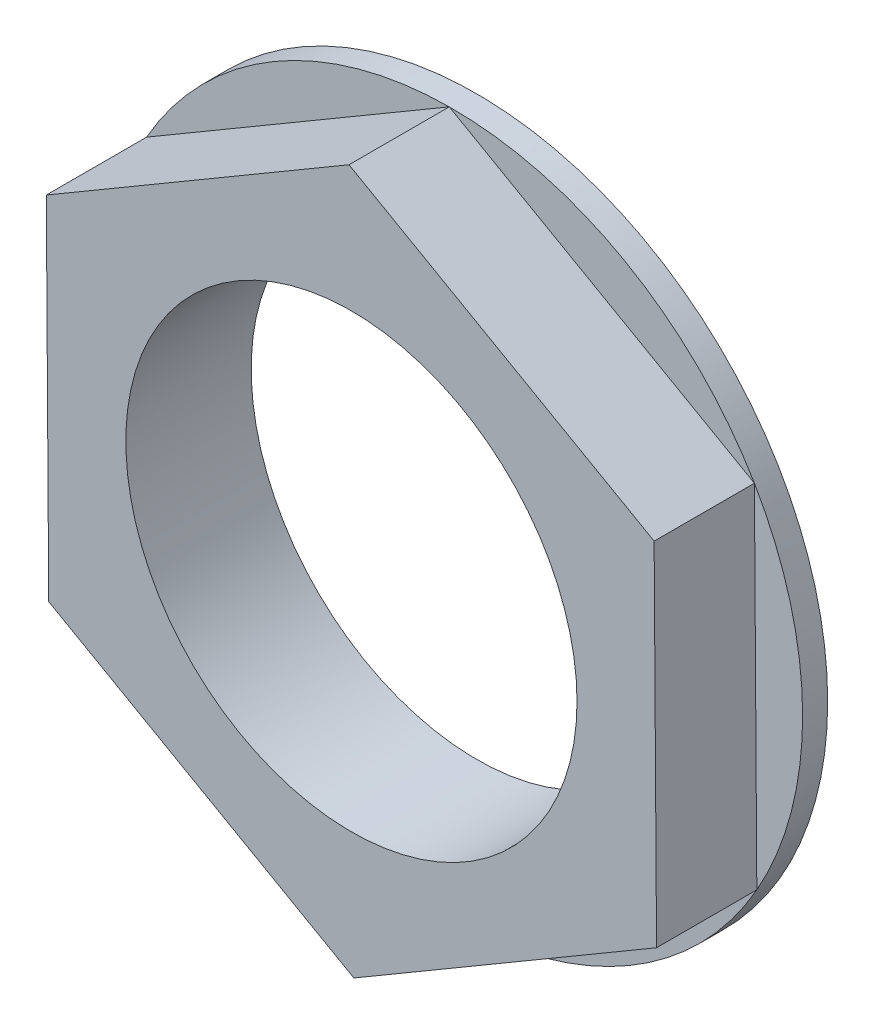
SolidWorks part; units mm, degrees
ref_plane "Plan de face" through (0, 0, 0) normal (0, 0, 1) x (1, 0, 0)
ref_plane "Plan de dessus" through (0, 0, 0) normal (0, 1, 0) x (1, 0, 0)
ref_plane "Plan de droite" through (0, 0, 0) normal (1, 0, 0) x (0, 0, -1)
sketch "Esquisse1" plane through (0, 0, 0) normal (0, 0, 1) x (1, 0, 0)
  circle A0 centre (0, 0) radius 4.5
  circle A1 centre (0, 0) radius 7
  dimension "D1" = 9
  dimension "D2" = 14
extrude "Boss.-Extru.1" add sketch "Esquisse1" along normal blind 0.5
sketch "Esquisse2" plane through (0, 0, 0.5) normal (0, 0, 1) x (1, 0, 0)
  line L1 (6.0862, -3.458) -> (6.0378, 3.5418)
  line L2 (6.0378, 3.5418) -> (-0.0484, 6.9998)
  line L3 (-0.0484, 6.9998) -> (-6.0862, 3.458)
  line L4 (-6.0862, 3.458) -> (-6.0378, -3.5418)
  line L5 (-6.0378, -3.5418) -> (0.0484, -6.9998)
  line L6 (0.0484, -6.9998) -> (6.0862, -3.458)
  circle A0 centre (0, 0) radius 4.5
  circle A1 centre (0, 0) radius 6.0622 construction
extrude "Boss.-Extru.2" add sketch "Esquisse2" along normal blind 2
